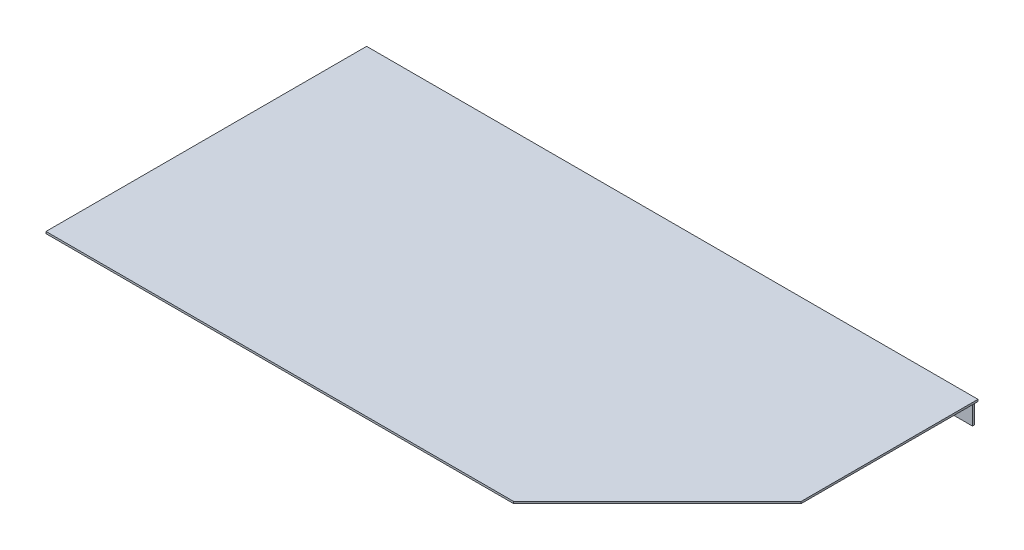
SolidWorks part; units mm, degrees
material "PPS"
ref_plane "Płaszczyzna XY" through (0, 0, 0) normal (0, 0, 1) x (1, 0, 0)
ref_plane "Płaszczyzna XZ" through (0, 0, 0) normal (0, 1, 0) x (1, 0, 0)
ref_plane "Płaszczyzna YZ" through (0, 0, 0) normal (1, 0, 0) x (0, 0, -1)
sketch "Szkic2" plane through (0, 0, 0) normal (0, 0, 1) x (1, 0, 0)
  line L0 (-276.5, 0) -> (276.5, 0)
  line L1 (-276.5, 0) -> (-276.5, -1.75)
  line L2 (276.5, 0) -> (276.5, -1.75)
  line L3 (276.5, -1.75) -> (-276.5, -1.75)
  point P4 (0, 0)
  dimension "D1" = 553
  dimension "D2" = 1.75
  dimension "D3" = 90
  dimension "D4" = 90
extrude "Dodanie-wyciągnięcie1" add sketch "Szkic2" along normal blind 290
sketch "Szkic3" plane through (0, 0, 0) normal (0, 1, 0) x (1, 0, 0)
  line L1 (276.5, -290) -> (-276.5, -290) construction
  line L5 (276.5, -290) -> (146.5, -290)
  line L6 (146.5, -290) -> (276.5, -160)
  line L7 (276.5, -290) -> (276.5, 0) construction
  line L8 (276.5, -160) -> (276.5, -290)
  dimension "D3" = 130
  dimension "D4" = 130
extrude "Wytnij-wyciągnięcie1" cut sketch "Szkic3" against normal blind 10
sketch "Szkic4" plane through (0, 0, 0) normal (0, 1, 0) x (1, 0, 0)
  line L0 (-276.5, -290) -> (146.5, -290)
  line L1 (-276.5, -290) -> (-276.5, 0) construction
  line L2 (146.5, -290) -> (-276.5, -290) construction
  line L3 (276.5, -160) -> (146.5, -290) construction
  line L4 (146.5, -290) -> (276.5, -160)
  line L5 (276.5, -160) -> (276.5, 0) construction
  line L6 (276.5, -160) -> (276.5, -157.1716)
  line L7 (276.5, -157.1716) -> (145.6716, -288)
  line L8 (145.6716, -288) -> (-276.5, -288)
  line L9 (-276.5, -288) -> (-276.5, -290)
  dimension "D1" = 2
  dimension "D2" = 2
sketch "Szkic5" plane through (0, -1.75, 0) normal (0, -1, 0) x (1, 0, 0)
  line L0 (-274.75, 0) -> (-274.75, 1.75)
  line L1 (-276.5, 0) -> (276.5, 0) construction
  line L2 (-274.75, 1.75) -> (273.25, 1.75)
  line L3 (273.25, 1.75) -> (273.25, 0)
  line L4 (273.25, 0) -> (-274.75, 0)
  line L5 (-276.5, 290) -> (-276.5, 0) construction
  point P6 (-274.75, 0.875)
  dimension "D1" = 1.75
  dimension "D2" = 1.75
  dimension "D3" = 548
  dimension "D4" = 548
extrude "Dodanie-wyciągnięcie2" add sketch "Szkic5" along normal blind 20
